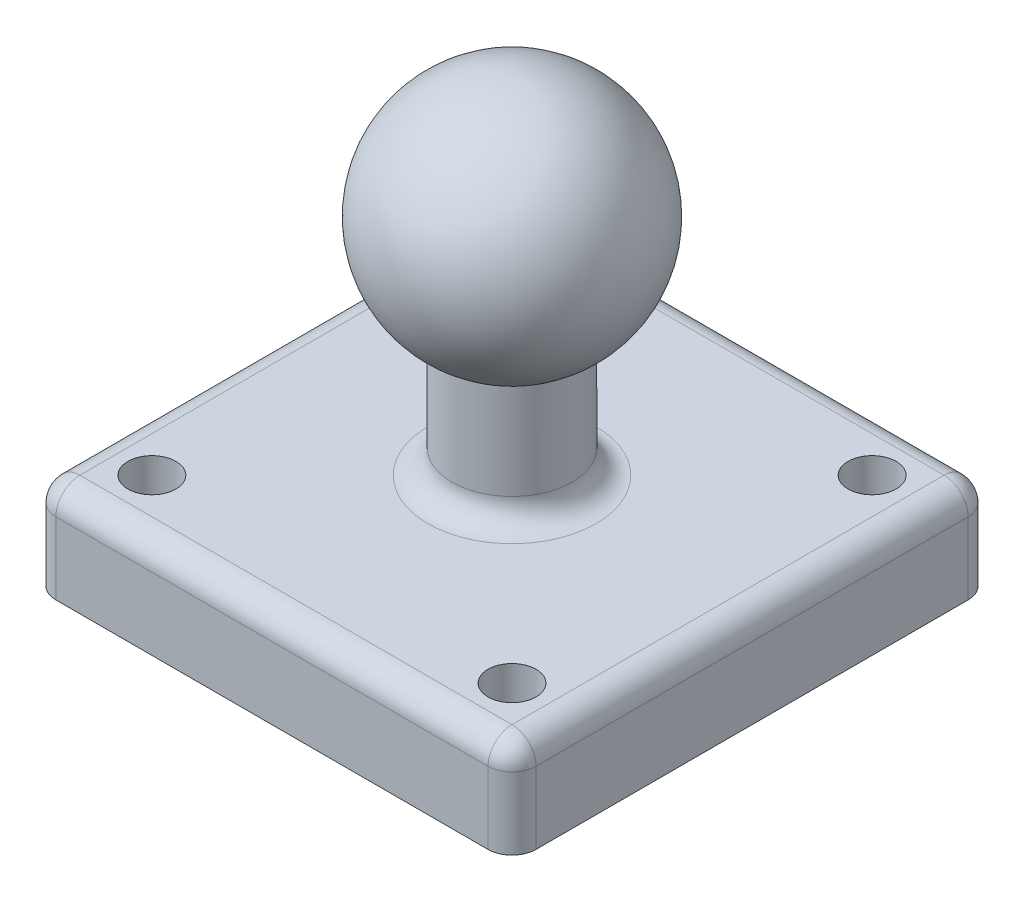
SolidWorks part; units mm, degrees
ref_plane "Plan de face" through (0, 0, 0) normal (0, 0, 1) x (1, 0, 0)
ref_plane "Plan de dessus" through (0, 0, 0) normal (0, 1, 0) x (1, 0, 0)
ref_plane "Plan de droite" through (0, 0, 0) normal (1, 0, 0) x (0, 0, -1)
sketch "Esquisse1" plane through (0, 0, 0) normal (0, 0, 1) x (1, 0, 0)
  line L0 (-2.5, -4.3301) -> (-2.5, -9.3301)
  line L1 (-2.5, -9.3301) -> (0, -9.3301)
  line L2 (0, -9.3301) -> (0, 5)
  line L3 (0, 5) -> (-7.2649, 5) construction
  arc A0 (0, 5) -> (-2.5, -4.3301) centre (0, 0) ccw
  dimension "D1" = 5
  dimension "D2" = 5
  dimension "D3" = 2.5
revolve "Révolution1" add sketch "Esquisse1" angle 360 about L2
sketch "Esquisse2" plane through (0, -9.3301, 0) normal (0, -1, 0) x (1, 0, 0)
  line L1 (-10, 10) -> (10, 10)
  line L2 (-10, 10) -> (-10, -10)
  line L3 (-10, -10) -> (10, -10)
  line L4 (10, 10) -> (10, -10)
  circle A0 centre (0, 0) radius 2.5 construction
  dimension "D3" = 10
  dimension "D4" = 10
  dimension "D1" = 20
  dimension "D2" = 20
extrude "Boss.-Extru.1" add sketch "Esquisse2" along normal blind 4
sketch "Esquisse3" plane through (0, -9.3301, 0) normal (0, 1, 0) x (1, 0, 0)
  circle A0 centre (7.5, -7.5) radius 1
  circle A1 centre (7.5, 7.5) radius 1
  circle A2 centre (-7.5, 7.5) radius 1
  circle A3 centre (-7.5, -7.5) radius 1
  circle A4 centre (0, 0) radius 2.5 construction
  dimension "D1" = 2
  dimension "D2" = 15
  dimension "D3" = 15
  dimension "D4" = 7.5
  dimension "D5" = 7.5
extrude "Enlèv. mat.-Extru.1" cut sketch "Esquisse3" against normal up to next
fillet "Congé1" radius 1 9 edges at (-10, -11.3301, -10) (2.5, -9.3301, 0) (-10, -9.3301, 0) (0, -9.3301, -10) (10, -11.3301, -10) (10, -11.3301, 10) (0, -9.3301, 10) (10, -9.3301, 0) (-10, -11.3301, 10)
